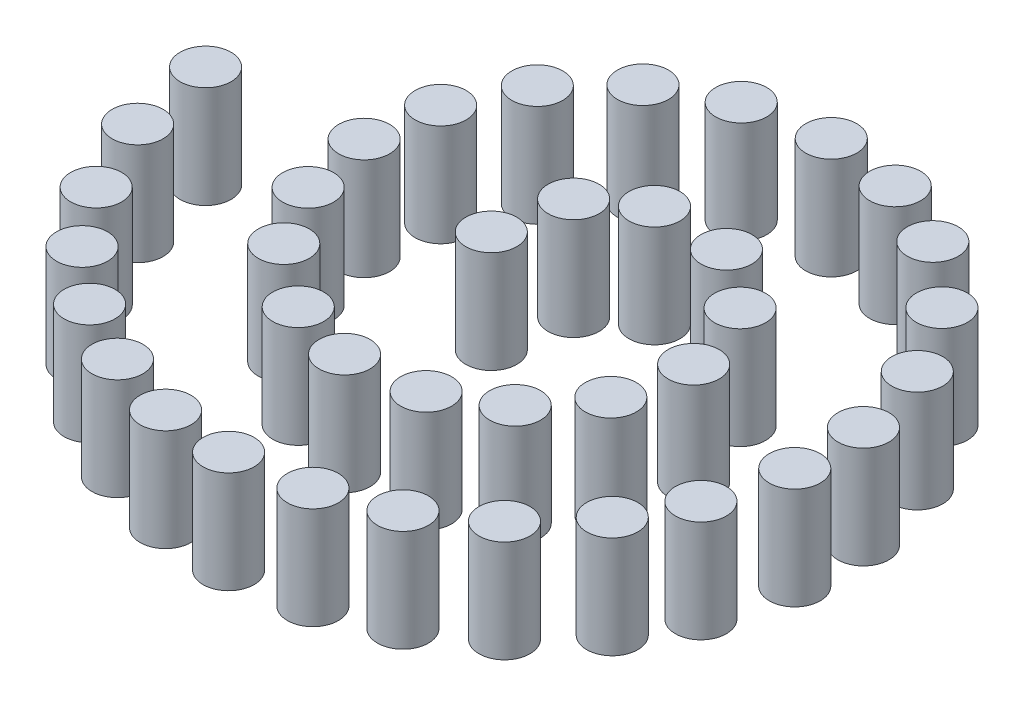
SolidWorks part; units mm, degrees
ref_plane "前基準面" through (0, 0, 0) normal (0, 0, 1) x (1, 0, 0)
ref_plane "上基準面" through (0, 0, 0) normal (0, 1, 0) x (1, 0, 0)
ref_plane "右基準面" through (0, 0, 0) normal (1, 0, 0) x (0, 0, -1)
sketch "草圖2" plane through (0, 0, 0) normal (0, 1, 0) x (1, 0, 0)
  circle A0 centre (0, 0) radius 70
  dimension "D1" = 140
curve "螺旋曲線/渦捲線1"
sketch "草圖3" plane through (0, 0, 0) normal (0, 1, 0) x (1, 0, 0)
  circle A0 centre (-350, 0) radius 25
  circle A1 centre (-334.8266, -81.7569) radius 25
  circle A2 centre (-301.6089, -155.6131) radius 25
  circle A3 centre (-258.1565, -212.9192) radius 25
  circle A4 centre (-205.5846, -258.12) radius 25
  circle A5 centre (-145.3072, -291.0619) radius 25
  circle A6 centre (-78.491, -310.7531) radius 25
  circle A7 centre (-11.8411, -315.6134) radius 25
  circle A8 centre (59.9658, -304.8298) radius 25
  circle A9 centre (123.2196, -279.8298) radius 25
  circle A10 centre (182.0054, -239.1156) radius 25
  circle A11 centre (231.369, -182.8541) radius 25
  circle A12 centre (261.2553, -125.8919) radius 25
  circle A13 centre (279.3067, -51.9552) radius 25
  circle A14 centre (278.1942, 16.477) radius 25
  circle A15 centre (257.0441, 90.3695) radius 25
  circle A16 centre (215.0822, 156.4855) radius 25
  circle A17 centre (154.455, 208.1826) radius 25
  circle A18 centre (88.8938, 236.8685) radius 25
  circle A19 centre (17.1596, 245.9541) radius 25
  circle A20 centre (-57.6503, 232.5453) radius 25
  circle A21 centre (-120.6011, 199.2077) radius 25
  circle A22 centre (-171.62, 146.6713) radius 25
  circle A23 centre (-202.3898, 82.7322) radius 25
  circle A24 centre (-211.0928, 16.477) radius 25
  circle A25 centre (-197.5514, -51.9552) radius 25
  circle A26 centre (-161.7447, -111.6503) radius 25
  circle A27 centre (-101.0782, -158.1275) radius 25
  circle A28 centre (-38.1627, -175.6689) radius 25
  circle A29 centre (33.4183, -167.3021) radius 25
  circle A30 centre (88.8938, -135.5083) radius 25
  circle A31 centre (128.8489, -81.7569) radius 25
  circle A32 centre (141.4569, -13.182) radius 25
  circle A33 centre (116.4569, 57.3353) radius 25
  circle A34 centre (59.9658, 100.454) radius 25
  circle A35 centre (-11.8411, 101.7309) radius 25
  circle A36 centre (-57.6503, 68.3017) radius 25
  circle A37 centre (-70, 0) radius 25
  spline S0 degree 3 poles (-691.2981, 2900.6628) (447.9149, -117.9357) (-58.2577, -140.0844) (-73.4266, 19.5686) (-73.3806, 24.8164) (-72.1304, 35.4562) (-70.9259, 40.8479) (-67.3059, 51.5156) (-64.8901, 56.7911) (-58.8535, 66.9525) (-55.2326, 71.838) (-46.8534, 80.9446) (-42.0952, 85.1653) (-31.5713, 92.6815) (-25.8058, 95.9764) (-13.4561, 101.4067) (-6.8722, 103.5417) (6.8722, 106.4583) (14.0325, 107.2396) (28.6435, 107.3071) (36.094, 106.593) (50.9665, 103.5896) (58.3882, 101.3) (72.8653, 95.1346) (79.9201, 91.2587) (93.3211, 81.9825) (99.6667, 76.5822) (111.3187, 64.3937) (116.6245, 57.6055) (125.8939, 42.8489) (129.8569, 34.8807) (136.1811, 18.0376) (138.5417, 9.163) (141.4583, -9.163) (142.014, -18.6139) (141.1877, -37.7184) (139.8054, -47.3715) (135.0487, -66.4768) (131.6742, -75.9285) (122.9634, -94.2149) (117.6272, -103.049) (105.1114, -119.6896) (97.9319, -127.4955) (81.934, -141.6928) (73.1158, -148.0837) (54.1264, -159.1063) (43.9556, -163.7375) (22.619, -170.9554) (11.4537, -173.5417) (-11.4537, -176.4583) (-23.1953, -176.7884) (-46.7933, -175.0683) (-58.649, -173.0178) (-81.9871, -166.5079) (-93.4688, -162.0483) (-115.5645, -150.7922) (-126.178, -143.9958) (-146.0582, -128.2403) (-155.3243, -119.2815) (-172.0669, -99.4742) (-179.5428, -88.6261) (-192.3187, -65.404) (-197.6181, -53.0305) (-205.7298, -27.2004) (-208.5417, -13.7445) (-211.4583, 13.7445) (-211.5628, 27.7768) (-208.9489, 55.8682) (-206.2303, 69.9266) (-197.967, 97.4974) (-192.4224, 111.009) (-178.6209, 136.9142) (-170.3643, 149.3069) (-151.3693, 172.4267) (-140.6312, 183.153) (-117.0145, 202.441) (-104.1364, 211.002) (-76.6815, 225.5311) (-62.1054, 231.4987) (-39.3627, 238.2528) (-31.6361, 240.1388) (-15.9635, 243.1478) (-8.0176, 244.2708) (8.0176, 245.7292) (16.1069, 246.0644) (32.3503, 245.93) (40.5044, 245.4603) (56.7969, 243.7064) (64.9352, 242.4223) (81.1143, 239.0383) (89.155, 236.9386) (105.0568, 231.9303) (112.9178, 229.0219) (128.3784, 222.4116) (135.9779, 218.7098) (150.8352, 210.5364) (158.0929, 206.0648) (172.1881, 196.3837) (179.0257, 191.1742) (192.2054, 180.0569) (198.5475, 174.1491) (210.6649, 161.6828) (216.4401, 155.1243) (227.3568, 141.4113) (232.4982, 134.2568) (242.0857, 119.4136) (246.5317, 111.7248) (254.6729, 95.881) (258.3681, 87.726) (264.9587, 71.0235) (267.8541, 62.476) (272.8038, 45.0675) (274.858, 36.2065) (278.0915, 18.2542) (279.2708, 9.163) (280.7292, -9.163) (281.0082, -18.3976) (280.6492, -36.9208) (280.0112, -46.2092) (277.8104, -64.7484) (276.2477, -73.9991) (272.1988, -92.3703) (269.7127, -101.4908) (263.8278, -119.5089) (260.429, -128.4066) (252.7389, -145.8874) (248.4476, -154.4706) (239.0015, -171.2325) (233.8468, -179.4113) (222.7125, -195.2773) (216.7328, -202.9645) (203.9957, -217.764) (197.2383, -224.8763) (183.0012, -238.4469) (175.5216, -244.9052) (159.9039, -257.0946) (151.7658, -262.8255) (134.9023, -273.4928) (126.1769, -278.4292) (108.2167, -287.447) (98.982, -291.5285) (80.0874, -298.7841) (70.4275, -301.9581) (50.7723, -307.3547) (40.777, -309.5772) (20.545, -313.0353) (10.3084, -314.2708) (-10.3084, -315.7292) (-20.6884, -315.9519) (-41.4912, -315.3684) (-51.914, -314.5621) (-72.6999, -311.9145) (-83.063, -310.0731) (-103.6263, -305.3592) (-113.8265, -302.4868) (-133.961, -295.7252) (-143.8953, -291.8362) (-163.3964, -283.0662) (-172.9632, -278.1853) (-191.6298, -267.4666) (-200.7296, -261.6288) (-218.3664, -249.0412) (-226.9034, -242.2915) (-243.3227, -227.9345) (-251.205, -220.3274) (-266.2289, -204.3196) (-273.3703, -195.9189) (-286.8323, -178.3965) (-293.1528, -169.2748) (-304.9, -150.3911) (-310.3267, -140.629) (-320.2211, -120.5524) (-324.6889, -110.238) (-332.6095, -89.1513) (-336.0622, -78.3791) (-341.9056, -56.4771) (-344.2964, -45.3474) (-412.7862, 373.3303) (240.4505, 946.0268) (2240.7166, -897.1919) knots -0.461866 -0.461866 -0.461866 -0.461866 0.015625 0.015625 0.03125 0.03125 0.046875 0.046875 0.0625 0.0625 0.078125 0.078125 0.09375 0.09375 0.109375 0.109375 0.125 0.125 0.140625 0.140625 0.15625 0.15625 0.171875 0.171875 0.1875 0.1875 0.203125 0.203125 0.21875 0.21875 0.234375 0.234375 0.25 0.25 0.265625 0.265625 0.28125 0.28125 0.296875 0.296875 0.3125 0.3125 0.328125 0.328125 0.34375 0.34375 0.359375 0.359375 0.375 0.375 0.390625 0.390625 0.40625 0.40625 0.421875 0.421875 0.4375 0.4375 0.453125 0.453125 0.46875 0.46875 0.484375 0.484375 0.5 0.5 0.515625 0.515625 0.53125 0.53125 0.546875 0.546875 0.5625 0.5625 0.578125 0.578125 0.59375 0.59375 0.609375 0.609375 0.617187 0.617187 0.625 0.625 0.632812 0.632812 0.640625 0.640625 0.648437 0.648437 0.65625 0.65625 0.664062 0.664062 0.671875 0.671875 0.679687 0.679687 0.6875 0.6875 0.695312 0.695312 0.703125 0.703125 0.710937 0.710937 0.71875 0.71875 0.726562 0.726562 0.734375 0.734375 0.742187 0.742187 0.75 0.75 0.757812 0.757812 0.765625 0.765625 0.773437 0.773437 0.78125 0.78125 0.789062 0.789062 0.796875 0.796875 0.804687 0.804687 0.8125 0.8125 0.820312 0.820312 0.828125 0.828125 0.835937 0.835937 0.84375 0.84375 0.851562 0.851562 0.859375 0.859375 0.867187 0.867187 0.875 0.875 0.882812 0.882812 0.890625 0.890625 0.898437 0.898437 0.90625 0.90625 0.914062 0.914062 0.921875 0.921875 0.929687 0.929687 0.9375 0.9375 0.945312 0.945312 0.953125 0.953125 0.960937 0.960937 0.96875 0.96875 0.976562 0.976562 0.984375 0.984375 0.992188 0.992188 1.274972 1.274972 1.274972 1.274972 only from (-70, 0) to (-350, 0) construction
  spline S1 degree 3 poles (-70, 0) (-71.4583, 4.5815) (-72.4653, 9.451) (-73.4266, 19.5686) (-73.3806, 24.8164) (-72.1304, 35.4562) (-70.9259, 40.8479) (-67.3059, 51.5156) (-64.8901, 56.7911) (-58.8535, 66.9525) (-55.2326, 71.838) (-46.8534, 80.9446) (-42.0952, 85.1653) (-31.5713, 92.6815) (-25.8058, 95.9764) (-13.4561, 101.4067) (-6.8722, 103.5417) (6.8722, 106.4583) (14.0325, 107.2396) (28.6435, 107.3071) (36.094, 106.593) (50.9665, 103.5896) (58.3882, 101.3) (72.8653, 95.1346) (79.9201, 91.2587) (93.3211, 81.9825) (99.6667, 76.5822) (111.3187, 64.3937) (116.6245, 57.6055) (125.8939, 42.8489) (129.8569, 34.8807) (136.1811, 18.0376) (138.5417, 9.163) (141.4583, -9.163) (142.014, -18.6139) (141.1877, -37.7184) (139.8054, -47.3715) (135.0487, -66.4768) (131.6742, -75.9285) (122.9634, -94.2149) (117.6272, -103.049) (105.1114, -119.6896) (97.9319, -127.4955) (81.934, -141.6928) (73.1158, -148.0837) (54.1264, -159.1063) (43.9556, -163.7375) (22.619, -170.9554) (11.4537, -173.5417) (-11.4537, -176.4583) (-23.1953, -176.7884) (-46.7933, -175.0683) (-58.649, -173.0178) (-81.9871, -166.5079) (-93.4688, -162.0483) (-115.5645, -150.7922) (-126.178, -143.9958) (-146.0582, -128.2403) (-155.3243, -119.2815) (-172.0669, -99.4742) (-179.5428, -88.6261) (-192.3187, -65.404) (-197.6181, -53.0305) (-205.7298, -27.2004) (-208.5417, -13.7445) (-211.4583, 13.7445) (-211.5628, 27.7768) (-208.9489, 55.8682) (-206.2303, 69.9266) (-197.967, 97.4974) (-192.4224, 111.009) (-178.6209, 136.9142) (-170.3643, 149.3069) (-151.3693, 172.4267) (-140.6312, 183.153) (-117.0145, 202.441) (-104.1364, 211.002) (-76.6815, 225.5311) (-62.1054, 231.4987) (-39.3627, 238.2528) (-31.6361, 240.1388) (-15.9635, 243.1478) (-8.0176, 244.2708) (8.0176, 245.7292) (16.1069, 246.0644) (32.3503, 245.93) (40.5044, 245.4603) (56.7969, 243.7064) (64.9352, 242.4223) (81.1143, 239.0383) (89.155, 236.9386) (105.0568, 231.9303) (112.9178, 229.0219) (128.3784, 222.4116) (135.9779, 218.7098) (150.8352, 210.5364) (158.0929, 206.0648) (172.1881, 196.3837) (179.0257, 191.1742) (192.2054, 180.0569) (198.5475, 174.1491) (210.6649, 161.6828) (216.4401, 155.1243) (227.3568, 141.4113) (232.4982, 134.2568) (242.0857, 119.4136) (246.5317, 111.7248) (254.6729, 95.881) (258.3681, 87.726) (264.9587, 71.0235) (267.8541, 62.476) (272.8038, 45.0675) (274.858, 36.2065) (278.0915, 18.2542) (279.2708, 9.163) (280.7292, -9.163) (281.0082, -18.3976) (280.6492, -36.9208) (280.0112, -46.2092) (277.8104, -64.7484) (276.2477, -73.9991) (272.1988, -92.3703) (269.7127, -101.4908) (263.8278, -119.5089) (260.429, -128.4066) (252.7389, -145.8874) (248.4476, -154.4706) (239.0015, -171.2325) (233.8468, -179.4113) (222.7125, -195.2773) (216.7328, -202.9645) (203.9957, -217.764) (197.2383, -224.8763) (183.0012, -238.4469) (175.5216, -244.9052) (159.9039, -257.0946) (151.7658, -262.8255) (134.9023, -273.4928) (126.1769, -278.4292) (108.2167, -287.447) (98.982, -291.5285) (80.0874, -298.7841) (70.4275, -301.9581) (50.7723, -307.3547) (40.777, -309.5772) (20.545, -313.0353) (10.3084, -314.2708) (-10.3084, -315.7292) (-20.6884, -315.9519) (-41.4912, -315.3684) (-51.914, -314.5621) (-72.6999, -311.9145) (-83.063, -310.0731) (-103.6263, -305.3592) (-113.8265, -302.4868) (-133.961, -295.7252) (-143.8953, -291.8362) (-163.3964, -283.0662) (-172.9632, -278.1853) (-191.6298, -267.4666) (-200.7296, -261.6288) (-218.3664, -249.0412) (-226.9034, -242.2915) (-243.3227, -227.9345) (-251.205, -220.3274) (-266.2289, -204.3196) (-273.3703, -195.9189) (-286.8323, -178.3965) (-293.1528, -169.2748) (-304.9, -150.3911) (-310.3267, -140.629) (-320.2211, -120.5524) (-324.6889, -110.238) (-332.6095, -89.1513) (-336.0622, -78.3791) (-341.9056, -56.4771) (-344.2964, -45.3474) (-347.979, -22.8357) (-349.2708, -11.4537) (-350, 0) knots 0 0 0 0 0.015625 0.015625 0.03125 0.03125 0.046875 0.046875 0.0625 0.0625 0.078125 0.078125 0.09375 0.09375 0.109375 0.109375 0.125 0.125 0.140625 0.140625 0.15625 0.15625 0.171875 0.171875 0.1875 0.1875 0.203125 0.203125 0.21875 0.21875 0.234375 0.234375 0.25 0.25 0.265625 0.265625 0.28125 0.28125 0.296875 0.296875 0.3125 0.3125 0.328125 0.328125 0.34375 0.34375 0.359375 0.359375 0.375 0.375 0.390625 0.390625 0.40625 0.40625 0.421875 0.421875 0.4375 0.4375 0.453125 0.453125 0.46875 0.46875 0.484375 0.484375 0.5 0.5 0.515625 0.515625 0.53125 0.53125 0.546875 0.546875 0.5625 0.5625 0.578125 0.578125 0.59375 0.59375 0.609375 0.609375 0.617187 0.617187 0.625 0.625 0.632812 0.632812 0.640625 0.640625 0.648437 0.648437 0.65625 0.65625 0.664062 0.664062 0.671875 0.671875 0.679687 0.679687 0.6875 0.6875 0.695312 0.695312 0.703125 0.703125 0.710937 0.710937 0.71875 0.71875 0.726562 0.726562 0.734375 0.734375 0.742187 0.742187 0.75 0.75 0.757812 0.757812 0.765625 0.765625 0.773437 0.773437 0.78125 0.78125 0.789062 0.789062 0.796875 0.796875 0.804687 0.804687 0.8125 0.8125 0.820312 0.820312 0.828125 0.828125 0.835937 0.835937 0.84375 0.84375 0.851562 0.851562 0.859375 0.859375 0.867187 0.867187 0.875 0.875 0.882812 0.882812 0.890625 0.890625 0.898437 0.898437 0.90625 0.90625 0.914062 0.914062 0.921875 0.921875 0.929687 0.929687 0.9375 0.9375 0.945312 0.945312 0.953125 0.953125 0.960937 0.960937 0.96875 0.96875 0.976562 0.976562 0.984375 0.984375 0.992188 0.992188 1 1 1 1
  dimension "D1" = 50
extrude "填料-伸長1" add sketch "草圖3" along normal blind 100
